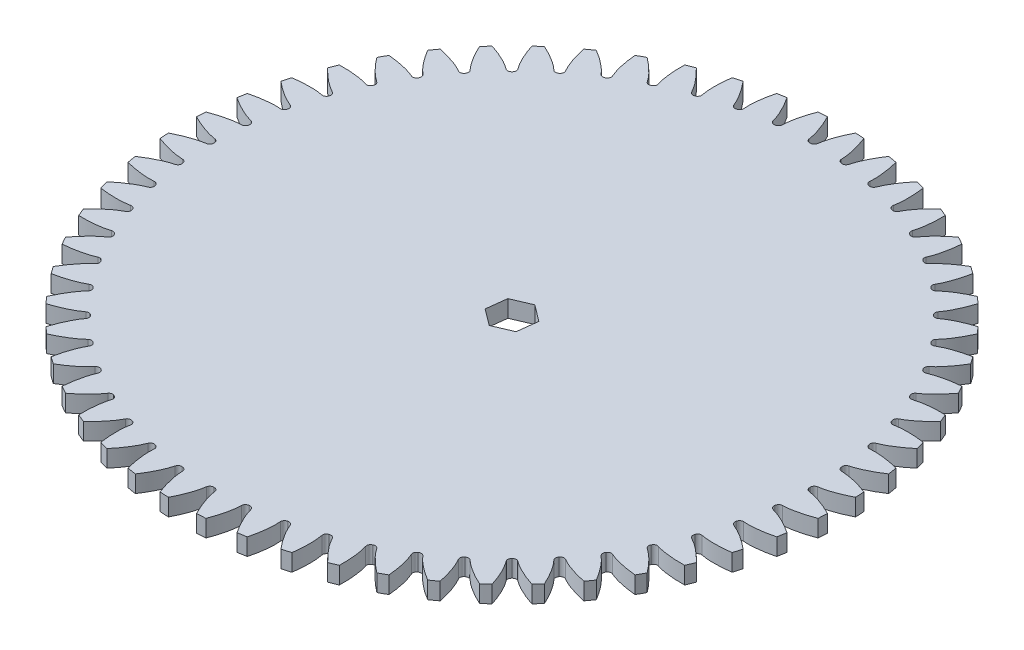
SolidWorks part; units mm, degrees
ref_plane "Front Plane" through (0, 0, 0) normal (0, 0, 1) x (1, 0, 0)
ref_plane "Top Plane" through (0, 0, 0) normal (0, 1, 0) x (1, 0, 0)
ref_plane "Right Plane" through (0, 0, 0) normal (1, 0, 0) x (0, 0, -1)
sketch "Sketch1" plane through (0, 0, 0) normal (0, 1, 0) x (1, 0, 0)
  circle A0 centre (0, 0) radius 122.7667
  dimension "D1" = 245.5333
extrude "Boss-Extrude1" add sketch "Sketch1" along normal blind 6.35
sketch "Sketch2" plane through (0, 6.35, 0) normal (0, 1, 0) x (1, 0, 0)
  line L0 (111.3753, 1.4642) -> (110.9461, 1.4585)
  line L1 (111.3753, -1.4642) -> (110.9461, -1.4585)
  line L2 (0, 0) -> (111.3753, 1.4642) construction
  line L3 (0, 0) -> (111.3753, -1.4642) construction
  arc A0 (122.6552, -5.2304) -> (122.6552, 5.2304) centre (0, 0) ccw
  circle A1 centre (0, 0) radius 118.5333 construction
  circle A2 centre (0, 0) radius 111.3849 construction
  circle A3 centre (0, 0) radius 110.9557 construction
  arc A4 (110.9461, -1.4585) -> (110.9461, 1.4585) centre (0, 0) ccw
  spline S0 degree 4 poles (111.3753, 1.4642) (111.393, 1.4646) (111.4426, 1.4663) (111.5363, 1.4715) (111.6892, 1.4832) (111.8839, 1.5025) (112.1356, 1.5325) (112.4319, 1.5744) (112.7573, 1.6273) (113.1113, 1.6923) (113.4642, 1.7637) (113.8161, 1.841) (114.1664, 1.9235) (114.5906, 2.0301) (115.0989, 2.1669) (115.6925, 2.34) (116.3651, 2.552) (117.0498, 2.7848) (117.723, 3.0276) (118.4024, 3.2888) (119.0592, 3.5527) (119.7407, 3.8431) (120.3692, 4.1194) (121.0725, 4.447) (121.6398, 4.7166) (122.387, 5.0915) (122.8281, 5.3187) (123.3438, 5.5911) (123.5726, 5.7157) (123.7135, 5.7922) knots 0 0 0 0 0 0.005377 0.015084 0.028532 0.04661 0.064855 0.092111 0.119476 0.146842 0.174209 0.201575 0.228941 0.256307 0.307035 0.361767 0.4165 0.471232 0.525964 0.580697 0.635429 0.690161 0.744894 0.799626 0.854358 0.909091 0.954545 1 1 1 1 1 construction
  spline S1 degree 4 poles (111.3753, 1.4642) (111.393, 1.4646) (111.4426, 1.4663) (111.5363, 1.4715) (111.6892, 1.4832) (111.8839, 1.5025) (112.1356, 1.5325) (112.4319, 1.5744) (112.7573, 1.6273) (113.1113, 1.6923) (113.4642, 1.7637) (113.8161, 1.841) (114.1664, 1.9235) (114.5906, 2.0301) (115.0989, 2.1669) (115.6925, 2.34) (116.3651, 2.552) (117.0498, 2.7848) (117.723, 3.0276) (118.4024, 3.2888) (119.0592, 3.5527) (119.7407, 3.8431) (120.3692, 4.1194) (121.0725, 4.447) (121.6398, 4.7166) (122.225, 5.0102) (122.5097, 5.1553) (122.6552, 5.2304) knots 0 0 0 0 0 0.005377 0.015084 0.028532 0.04661 0.064855 0.092111 0.119476 0.146842 0.174209 0.201575 0.228941 0.256307 0.307035 0.361767 0.4165 0.471232 0.525964 0.580697 0.635429 0.690161 0.744894 0.799626 0.854358 0.909091 0.909091 0.909091 0.909091 0.909091
  spline S2 degree 4 poles (111.3753, -1.4642) (111.393, -1.4646) (111.4426, -1.4663) (111.5363, -1.4715) (111.6892, -1.4832) (111.8839, -1.5025) (112.1356, -1.5325) (112.4319, -1.5744) (112.7573, -1.6273) (113.1113, -1.6923) (113.4642, -1.7637) (113.8161, -1.841) (114.1664, -1.9235) (114.5906, -2.0301) (115.0989, -2.1669) (115.6925, -2.34) (116.3651, -2.552) (117.0498, -2.7848) (117.723, -3.0276) (118.4024, -3.2888) (119.0592, -3.5527) (119.7407, -3.8431) (120.3692, -4.1194) (121.0725, -4.447) (121.6398, -4.7166) (122.387, -5.0915) (122.8281, -5.3187) (123.3438, -5.5911) (123.5726, -5.7157) (123.7135, -5.7922) knots 0 0 0 0 0 0.005377 0.015084 0.028532 0.04661 0.064855 0.092111 0.119476 0.146842 0.174209 0.201575 0.228941 0.256307 0.307035 0.361767 0.4165 0.471232 0.525964 0.580697 0.635429 0.690161 0.744894 0.799626 0.854358 0.909091 0.954545 1 1 1 1 1 construction
  spline S3 degree 4 poles (111.3753, -1.4642) (111.393, -1.4646) (111.4426, -1.4663) (111.5363, -1.4715) (111.6892, -1.4832) (111.8839, -1.5025) (112.1356, -1.5325) (112.4319, -1.5744) (112.7573, -1.6273) (113.1113, -1.6923) (113.4642, -1.7637) (113.8161, -1.841) (114.1664, -1.9235) (114.5906, -2.0301) (115.0989, -2.1669) (115.6925, -2.34) (116.3651, -2.552) (117.0498, -2.7848) (117.723, -3.0276) (118.4024, -3.2888) (119.0592, -3.5527) (119.7407, -3.8431) (120.3692, -4.1194) (121.0725, -4.447) (121.6398, -4.7166) (122.225, -5.0102) (122.5097, -5.1553) (122.6552, -5.2304) knots 0 0 0 0 0 0.005377 0.015084 0.028532 0.04661 0.064855 0.092111 0.119476 0.146842 0.174209 0.201575 0.228941 0.256307 0.307035 0.361767 0.4165 0.471232 0.525964 0.580697 0.635429 0.690161 0.744894 0.799626 0.854358 0.909091 0.909091 0.909091 0.909091 0.909091
  dimension "D2" = 237.0667
  dimension "D3" = 222.7698
  dimension "D4" = 221.9113
extrude "Cut-Extrude1" cut sketch "Sketch2" against normal up to next (6.35 mm away)
fillet "Fillet1" radius 1.4203 2 edges at (110.9461, 3.175, 1.4585) (110.9461, 3.175, -1.4585)
ref_axis "Axis1" through (0, 6.35, 0) along (0, -1, 0)
pattern_circular "CirPattern2" count 56 over 360 about axis through (0, 6.35, 0) along (0, -1, 0) of "Cut-Extrude1", "Fillet1"
sketch "Sketch3" plane through (0, 6.35, 0) normal (0, 1, 0) x (1, 0, 0)
  line L1 (-0.9082, -7.5714) -> (6.1029, -4.5722)
  line L2 (6.1029, -4.5722) -> (7.0111, 2.9992)
  line L3 (7.0111, 2.9992) -> (0.9082, 7.5714)
  line L4 (0.9082, 7.5714) -> (-6.1029, 4.5722)
  line L5 (-6.1029, 4.5722) -> (-7.0111, -2.9992)
  line L6 (-7.0111, -2.9992) -> (-0.9082, -7.5714)
  circle A0 centre (0, 0) radius 6.604 construction
extrude "Cut-Extrude2" cut sketch "Sketch3" against normal up to next
equation "\"DiametralPitch\" = 6"
equation "\"NumTeeth\"= 56"
equation "\"PressureAngle\"= 20"
equation "\"Addendum\"= 1 / \"DiametralPitch\""
equation "\"Dedendum\"= 1.25 / \"DiametralPitch\""
equation "\"WorkingDepth\"= 2 / \"DiametralPitch\""
equation "\"WholeDepth\"= 2.25 / \"DiametralPitch\""
equation "\"Clearance\"= 0.25 / \"DiametralPitch\""
equation "\"ToothThickness\"= 1.5708 / \"DiametralPitch\""
equation "\"CircularPitch\"= pi / \"DiametralPitch\""
equation "\"PitchCircle\"= \"NumTeeth\" / \"DiametralPitch\""
equation "\"OutsideDiameter\"= ( \"NumTeeth\" + 2 ) / \"DiametralPitch\""
equation "\"Fillet\"= \"Clearance\" * cos ( \"PressureAngle\" ) * tan ( ( 90 + \"PressureAngle\" ) / 2 )"
equation "\"AddendumCircle\"= \"PitchCircle\" + ( 2 * \"Addendum\" )"
equation "\"DedendumCircle\"= \"PitchCircle\" - ( 2 * \"Dedendum\" ) - .18"
equation "\"BaseCircle\"= \"PitchCircle\" * cos ( \"PressureAngle\" )"
equation "\"PitchAngle\"= 360deg / \"NumTeeth\""
equation "\"Alpha\"= sqr ( \"PitchCircle\" ^ 2 - \"BaseCircle\" ^ 2 ) / \"BaseCircle\" * 180 / PI - \"PressureAngle\""
equation "\"Beta\"= ( \"PitchAngle\" / 4 - \"Alpha\" )"
equation "\"Phi\"= sqr ( ( \"AddendumCircle\" / 2 ) ^ 2 - ( \"BaseCircle\" / 2 ) ^ 2 ) / ( \"BaseCircle\" / 2 )"
equation "\"D1@Sketch1\"=\"OutsideDiameter\""
equation "\"D2@Sketch2\"=\"PitchCircle\""
equation "\"D3@Sketch2\"=\"BaseCircle\""
equation "\"D4@Sketch2\"=\"DedendumCircle\""
equation "\"D1@Fillet1\"=\"Fillet\""
equation "\"D1@CirPattern2\"=\"NumTeeth\""
